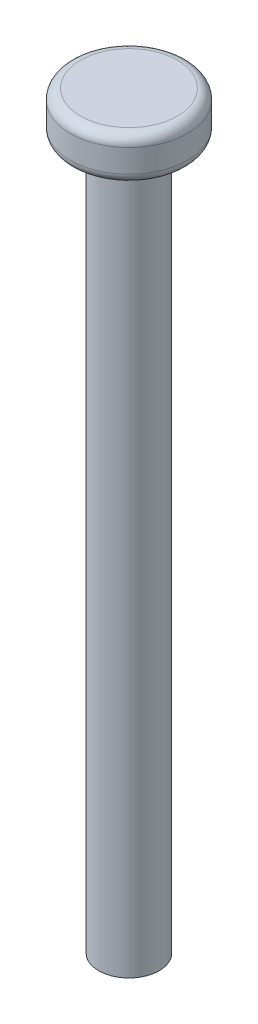
SolidWorks part; units mm, degrees
ref_plane "Спереди" through (0, 0, 0) normal (0, 0, 1) x (1, 0, 0)
ref_plane "Сверху" through (0, 0, 0) normal (0, 1, 0) x (1, 0, 0)
ref_plane "Справа" through (0, 0, 0) normal (1, 0, 0) x (0, 0, -1)
sketch "Sketch1" plane through (0, 0, 0) normal (0, 1, 0) x (1, 0, 0)
  circle A0 centre (0, 0) radius 3
  dimension "D1" = 6
extrude "Boss-Extrude1" add sketch "Sketch1" along normal blind 70
sketch "Sketch2" plane through (0, 70, 0) normal (0, 1, 0) x (1, 0, 0)
  circle A0 centre (0, 0) radius 5.8
  dimension "D1" = 11.6
extrude "Boss-Extrude2" add sketch "Sketch2" along normal blind 4.3
fillet "Fillet1" radius 1 2 edges at (0, 70, 5.8) (0, 74.3, 5.8)
